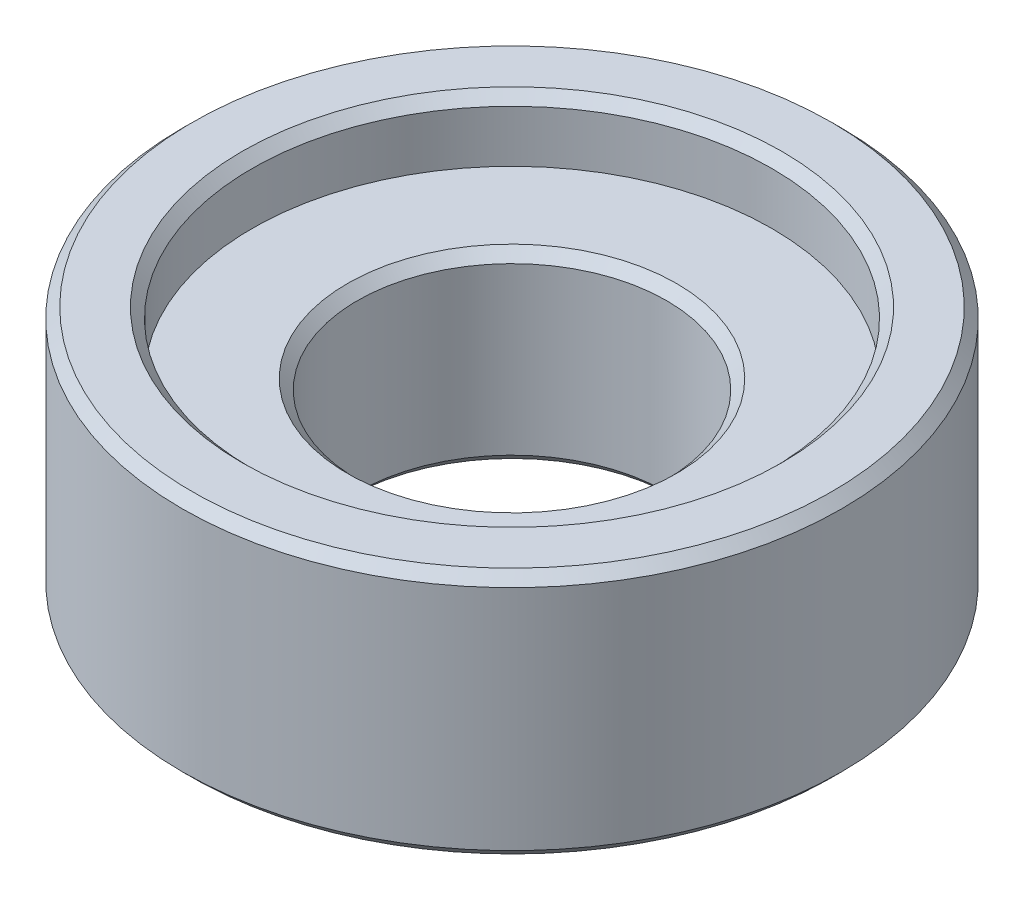
SolidWorks part; units mm, degrees
ref_plane "Front" through (0, 0, 0) normal (0, 0, 1) x (1, 0, 0)
ref_plane "Top" through (0, 0, 0) normal (0, 1, 0) x (1, 0, 0)
ref_plane "Right" through (0, 0, 0) normal (1, 0, 0) x (0, 0, -1)
sketch "Sketch1" plane through (0, 0, 0) normal (0, 0, 1) x (1, 0, 0)
  line L0 (16.4084, 12.7) -> (13.843, 12.7)
  line L1 (13.843, 12.7) -> (13.335, 12.192)
  line L2 (13.335, 12.192) -> (13.335, 9.525)
  line L3 (13.335, 9.525) -> (8.4455, 9.525)
  line L4 (8.4455, 9.525) -> (7.9375, 9.017)
  line L5 (7.9375, 9.017) -> (7.9375, 0.508)
  line L6 (7.9375, 0.508) -> (8.4455, 0)
  line L7 (8.4455, 0) -> (16.4084, 0)
  line L8 (16.4084, 0) -> (16.9164, 0.508)
  line L9 (16.9164, 0.508) -> (16.9164, 12.192)
  line L10 (16.9164, 12.192) -> (16.4084, 12.7)
  line L11 (0, 12.7) -> (0, 0) construction
revolve "Revolve1" add sketch "Sketch1" angle 360 about L11
